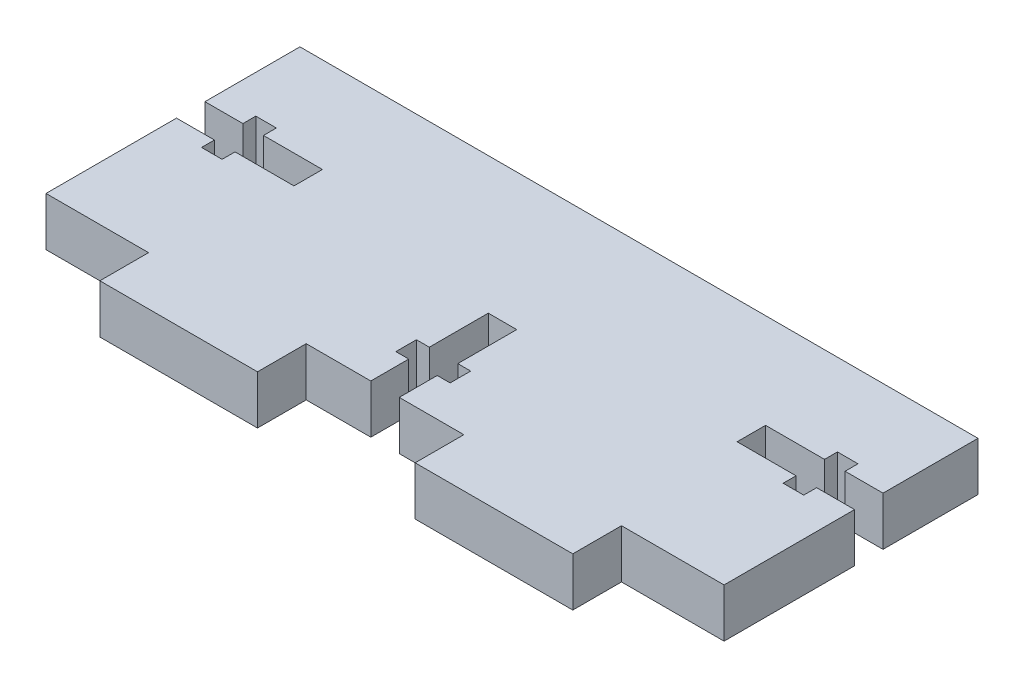
SolidWorks part; units mm, degrees
ref_plane "Front Plane" through (0, 0, 0) normal (0, 0, 1) x (1, 0, 0)
ref_plane "Top Plane" through (0, 0, 0) normal (0, 1, 0) x (1, 0, 0)
ref_plane "Right Plane" through (0, 0, 0) normal (1, 0, 0) x (0, 0, -1)
sketch "Sketch2" plane through (0, 0, 0) normal (0, 1, 0) x (1, 0, 0)
  line L0 (48.7718, 3.7488) -> (59.5718, 3.7488)
  line L1 (-1.0282, 3.7488) -> (-11.8282, 3.7488)
  line L2 (-11.8282, 17.4903) -> (-11.8282, 3.7488)
  line L3 (-11.8282, 30.4873) -> (59.5718, 30.4873)
  line L4 (-11.8282, 20.4873) -> (-11.8282, 30.4873)
  line L8 (25.3703, 3.7488) -> (32.1718, 3.7488)
  line L9 (25.3703, 3.7488) -> (25.3703, 7.7438)
  line L10 (22.3733, 7.7438) -> (22.3733, 3.7488)
  line L11 (21.0143, 7.7438) -> (22.3733, 7.7438)
  line L12 (22.3733, 9.9108) -> (21.0143, 9.9108)
  line L14 (21.0143, 9.9108) -> (21.0143, 7.7438)
  line L15 (25.3703, 7.7438) -> (26.7293, 7.7438)
  line L16 (26.7293, 9.9108) -> (25.3703, 9.9108)
  line L17 (26.7293, 7.7438) -> (26.7293, 9.9108)
  line L18 (25.3703, 16.1178) -> (22.3733, 16.1178)
  line L19 (22.3733, 16.1178) -> (22.3733, 9.9108)
  line L20 (25.3703, 9.9108) -> (25.3703, 16.1178)
  line L21 (22.3733, 3.7488) -> (15.5718, 3.7488)
  line L22 (32.1718, 3.7488) -> (32.1718, -1.3812)
  line L23 (15.5718, 3.7488) -> (15.5718, -1.3812)
  line L24 (32.1718, -1.3812) -> (48.7718, -1.3812)
  line L25 (15.5718, -1.3812) -> (-1.0282, -1.3812)
  line L26 (48.7718, -1.3812) -> (48.7718, 3.7488)
  line L27 (-1.0282, -1.3812) -> (-1.0282, 3.7488)
  line L35 (59.5718, 20.4873) -> (55.5768, 20.4873)
  line L36 (55.5768, 17.4903) -> (59.5718, 17.4903)
  line L37 (55.5768, 16.1313) -> (55.5768, 17.4903)
  line L38 (53.4098, 17.4903) -> (53.4098, 16.1313)
  line L39 (53.4098, 16.1313) -> (55.5768, 16.1313)
  line L40 (55.5768, 20.4873) -> (55.5768, 21.8463)
  line L41 (53.4098, 21.8463) -> (53.4098, 20.4873)
  line L42 (55.5768, 21.8463) -> (53.4098, 21.8463)
  line L43 (47.2028, 20.4873) -> (47.2028, 17.4903)
  line L44 (47.2028, 17.4903) -> (53.4098, 17.4903)
  line L45 (53.4098, 20.4873) -> (47.2028, 20.4873)
  line L46 (59.5718, 3.7488) -> (59.5718, 17.4903)
  line L47 (59.5718, 20.4873) -> (59.5718, 30.4873)
  line L48 (-11.8282, 17.4903) -> (-7.8332, 17.4903)
  line L49 (-7.8332, 20.4873) -> (-11.8282, 20.4873)
  line L50 (-7.8332, 21.8463) -> (-7.8332, 20.4873)
  line L51 (-5.6662, 20.4873) -> (-5.6662, 21.8463)
  line L52 (-5.6662, 21.8463) -> (-7.8332, 21.8463)
  line L53 (-7.8332, 17.4903) -> (-7.8332, 16.1313)
  line L54 (-5.6662, 16.1313) -> (-5.6662, 17.4903)
  line L55 (-7.8332, 16.1313) -> (-5.6662, 16.1313)
  line L56 (0.5408, 17.4903) -> (0.5408, 20.4873)
  line L57 (0.5408, 20.4873) -> (-5.6662, 20.4873)
  line L58 (-5.6662, 17.4903) -> (0.5408, 17.4903)
  dimension "D2" = 49.8
  dimension "D3" = 10.8
  dimension "D4" = 10.8
  dimension "D5" = 3.995
  dimension "D6" = 3.995
  dimension "D7" = 3.995
  dimension "D8" = 2.997
  dimension "D9" = 5.13
  dimension "D10" = 6.8015
  dimension "D11" = 3.995
  dimension "D12" = 3.995
  dimension "D13" = 13.7415
  dimension "D14" = 10
  dimension "D15" = 13.7415
  dimension "D16" = 2.167
  dimension "D17" = 2.167
  dimension "D18" = 71.4
  dimension "D19" = 10
  dimension "D30" = 16.6
  dimension "D31" = 16.6
  dimension "D32" = 5.13
  dimension "D33" = 6.8015
  dimension "D34" = 5.13
  dimension "D35" = 90
  dimension "D36" = 90
  dimension "D37" = 5.13
  dimension "D38" = 90
  dimension "D39" = 90
  dimension "D40" = 90
  dimension "D41" = 90
extrude "Boss-Extrude4" add sketch "Sketch2" along normal blind 5.13
